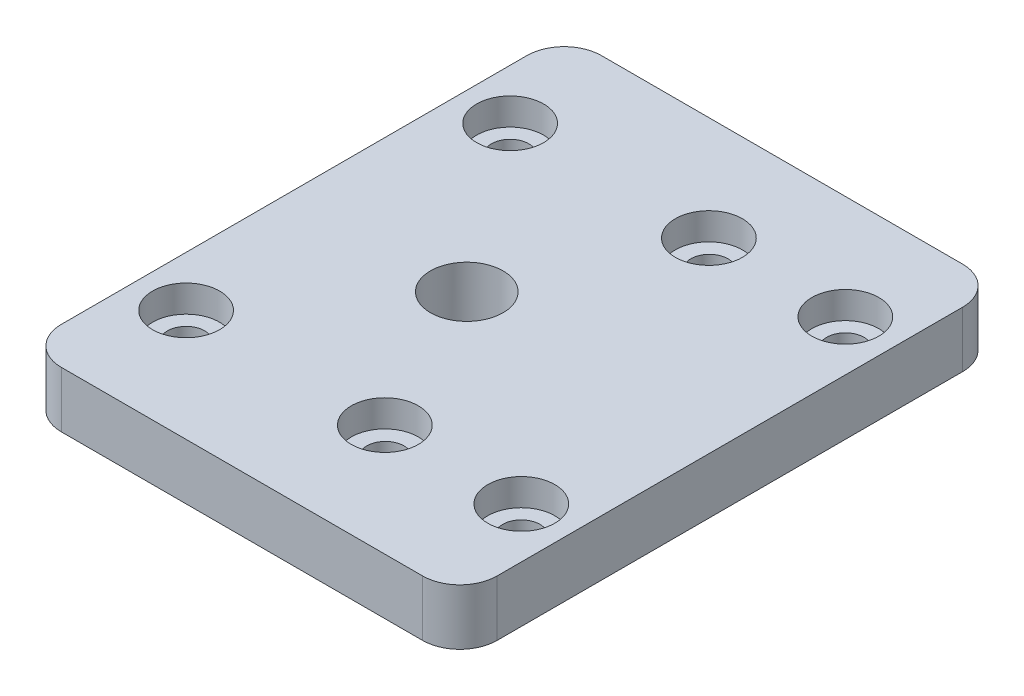
SolidWorks part; units mm, degrees
material "ABS"
ref_plane "Front Plane" through (0, 0, 0) normal (0, 0, 1) x (1, 0, 0)
ref_plane "Top Plane" through (0, 0, 0) normal (0, 1, 0) x (1, 0, 0)
ref_plane "Right Plane" through (0, 0, 0) normal (1, 0, 0) x (0, 0, -1)
other "Center of Mass"
sketch "Sketch1" plane through (0, 0, 0) normal (0, 1, 0) x (1, 0, 0)
  line L0 (-30.4611, 0) -> (33.997, 0) construction
  line L1 (-11.7, -14.5) -> (11.7, -14.5)
  line L2 (-11.7, -14.5) -> (-11.7, 14.5)
  line L3 (-11.7, 14.5) -> (11.7, 14.5)
  line L4 (11.7, -14.5) -> (11.7, 14.5)
  line L5 (-11.7, -14.5) -> (11.7, 14.5) construction
  line L6 (-11.7, 14.5) -> (11.7, -14.5) construction
  circle A0 centre (9, 8.9) radius 1
  circle A2 centre (9, -8.5) radius 1
  circle A3 centre (-9, -8.5) radius 1
  circle A5 centre (1.7, -8.5) radius 1
  spline S1 degree 3 poles (19.181, -14.2425) (19.8008, -12.3411) (17.8993, -11.7212) (17.2795, -13.6227) (16.6596, -15.5241) (18.5612, -16.144) (19.181, -14.2425) (19.8008, -12.3411) (17.8993, -11.7212) knots -0.5 0 0 0 0.5 0.5 0.5 1 1 1 1.5 1.5 1.5 weights 1 0.333333 0.333333 1 0.333333 0.333333 1 0.333333 0.333333 only from (19.181, -14.2425) to (19.181, -14.2425) construction
  spline S2 degree 3 poles (22.4885, -4.0962) (23.1083, -2.1947) (21.2068, -1.5749) (20.587, -3.4763) (19.9671, -5.3778) (21.8687, -5.9977) (22.4885, -4.0962) (23.1083, -2.1947) (21.2068, -1.5749) knots -0.5 0 0 0 0.5 0.5 0.5 1 1 1 1.5 1.5 1.5 weights 1 0.333333 0.333333 1 0.333333 0.333333 1 0.333333 0.333333 only from (22.4885, -4.0962) to (22.4885, -4.0962) construction
  spline S3 degree 3 poles (19.181, -14.2425) (19.8008, -12.3411) (17.8993, -11.7212) (17.2795, -13.6227) (16.6596, -15.5241) (18.5612, -16.144) (19.181, -14.2425) (19.8008, -12.3411) (17.8993, -11.7212) knots -0.5 0 0 0 0.5 0.5 0.5 1 1 1 1.5 1.5 1.5 weights 1 0.333333 0.333333 1 0.333333 0.333333 1 0.333333 0.333333 only from (19.181, -14.2425) to (19.181, -14.2425)
  spline S4 degree 3 poles (22.4885, -4.0962) (23.1083, -2.1947) (21.2068, -1.5749) (20.587, -3.4763) (19.9671, -5.3778) (21.8687, -5.9977) (22.4885, -4.0962) (23.1083, -2.1947) (21.2068, -1.5749) knots -0.5 0 0 0 0.5 0.5 0.5 1 1 1 1.5 1.5 1.5 weights 1 0.333333 0.333333 1 0.333333 0.333333 1 0.333333 0.333333 only from (22.4885, -4.0962) to (22.4885, -4.0962)
  point P0 (0, 0)
  point P6 (-9, 8.5)
  point P7 (9, 8.5)
  point P8 (9, 8.9)
  point P18 (1.7, 8.5)
  dimension "D7" = 17.4
  dimension "D8" = 18
  dimension "D10" = 2
  dimension "D1" = 29
  dimension "D2" = 23.4
  dimension "D3" = 6
  dimension "D4" = 6
  dimension "D5" = 18
  dimension "D6" = 2.7
  dimension "D9" = 10.7
extrude "Boss-Extrude1" add sketch "Sketch1" along normal blind 3
fillet "Fillet1" radius 2 4 edges at (11.7, 1.5, -14.5) (11.7, 1.5, 14.5) (-11.7, 1.5, 14.5) (-11.7, 1.5, -14.5)
sketch "Sketch5" plane through (0, 0, 0) normal (0, -1, 0) x (1, 0, 0)
  circle A0 centre (-2.1456, 3.6104) radius 2.5 construction
  circle A1 centre (-2.1456, 3.6104) radius 2.5 construction
  circle A2 centre (-2.1456, 3.6104) radius 1.44
  dimension "D1" = 2.88
extrude "Cut-Extrude3" cut sketch "Sketch5" against normal blind 10
sketch "Sketch7" plane through (0, 3, 0) normal (0, 1, 0) x (1, 0, 0)
  spline S0 degree 3 poles (19.181, -14.2425) (19.8008, -12.3411) (17.8993, -11.7212) (17.2795, -13.6227) (16.6596, -15.5241) (18.5612, -16.144) (19.181, -14.2425) (19.8008, -12.3411) (17.8993, -11.7212) knots -0.5 0 0 0 0.5 0.5 0.5 1 1 1 1.5 1.5 1.5 weights 1 0.333333 0.333333 1 0.333333 0.333333 1 0.333333 0.333333 only from (19.181, -14.2425) to (19.181, -14.2425) construction
  spline S1 degree 3 poles (22.4885, -4.0962) (23.1083, -2.1947) (21.2068, -1.5749) (20.587, -3.4763) (19.9671, -5.3778) (21.8687, -5.9977) (22.4885, -4.0962) (23.1083, -2.1947) (21.2068, -1.5749) knots -0.5 0 0 0 0.5 0.5 0.5 1 1 1 1.5 1.5 1.5 weights 1 0.333333 0.333333 1 0.333333 0.333333 1 0.333333 0.333333 only from (22.4885, -4.0962) to (22.4885, -4.0962) construction
  spline S2 degree 3 poles (19.181, -14.2425) (19.8008, -12.3411) (17.8993, -11.7212) (17.2795, -13.6227) (16.6596, -15.5241) (18.5612, -16.144) (19.181, -14.2425) (19.8008, -12.3411) (17.8993, -11.7212) knots -0.5 0 0 0 0.5 0.5 0.5 1 1 1 1.5 1.5 1.5 weights 1 0.333333 0.333333 1 0.333333 0.333333 1 0.333333 0.333333 only from (19.181, -14.2425) to (19.181, -14.2425)
  spline S3 degree 3 poles (22.4885, -4.0962) (23.1083, -2.1947) (21.2068, -1.5749) (20.587, -3.4763) (19.9671, -5.3778) (21.8687, -5.9977) (22.4885, -4.0962) (23.1083, -2.1947) (21.2068, -1.5749) knots -0.5 0 0 0 0.5 0.5 0.5 1 1 1 1.5 1.5 1.5 weights 1 0.333333 0.333333 1 0.333333 0.333333 1 0.333333 0.333333 only from (22.4885, -4.0962) to (22.4885, -4.0962)
extrude "Cut-Extrude4" cut sketch "Sketch7" against normal blind 10
sketch "Sketch8" plane through (0, 3, 0) normal (0, 1, 0) x (1, 0, 0)
  line L0 (24.633, 0) -> (-21.7502, 0) construction
  line L1 (1.7, -8.5) -> (1.7, 20.7764) construction
  line L2 (-9, -8.5) -> (-9, 21.3011) construction
  line L3 (9, -8.5) -> (9, 8.9) construction
  line L4 (14.3582, 8.9) -> (-23.7207, 8.9) construction
  circle A0 centre (1.7, 8.9) radius 1
  circle A1 centre (-9, 8.9) radius 1
  point P15 (1.7, 8.9)
  point P16 (-9, 8.9)
  dimension "D1" = 2
  dimension "D2" = 2
extrude "Cut-Extrude5" cut sketch "Sketch8" against normal blind 10
sketch "Sketch9" plane through (0, 3, 0) normal (0, 1, 0) x (1, 0, 0)
  circle A0 centre (-2.1456, -3.6104) radius 3.027
extrude "Boss-Extrude3" add sketch "Sketch9" against normal up to surface (3 mm away) up to face at (-9, 0, -9.9)
sketch "Sketch10" plane through (0, 3, 0) normal (0, 1, 0) x (1, 0, 0)
  circle A1 centre (-2.3282, -0.1) radius 1.5 construction
  circle A2 centre (-2.3282, -0.1) radius 1.95
  circle A3 centre (-2.3282, -0.1) radius 4 construction
  dimension "D1" = 3.9
extrude "Cut-Extrude6" cut sketch "Sketch10" against normal blind 10
sketch "Sketch11" plane through (0, 3, 0) normal (0, 1, 0) x (1, 0, 0)
  circle A0 centre (-9, -8.5) radius 1.8
  circle A1 centre (1.6718, -8.5) radius 1.8
  circle A2 centre (9, -8.5) radius 1.8
  circle A3 centre (9, 8.9) radius 1.8
  circle A4 centre (1.6718, 8.9) radius 1.8
  circle A5 centre (-9, 8.9) radius 1.8
  dimension "D1" = 3.6
  dimension "D2" = 3.6
  dimension "D3" = 3.6
  dimension "D4" = 3.6
  dimension "D5" = 3.6
  dimension "D6" = 3.6
extrude "Cut-Extrude7" cut sketch "Sketch11" against normal blind 1.45
